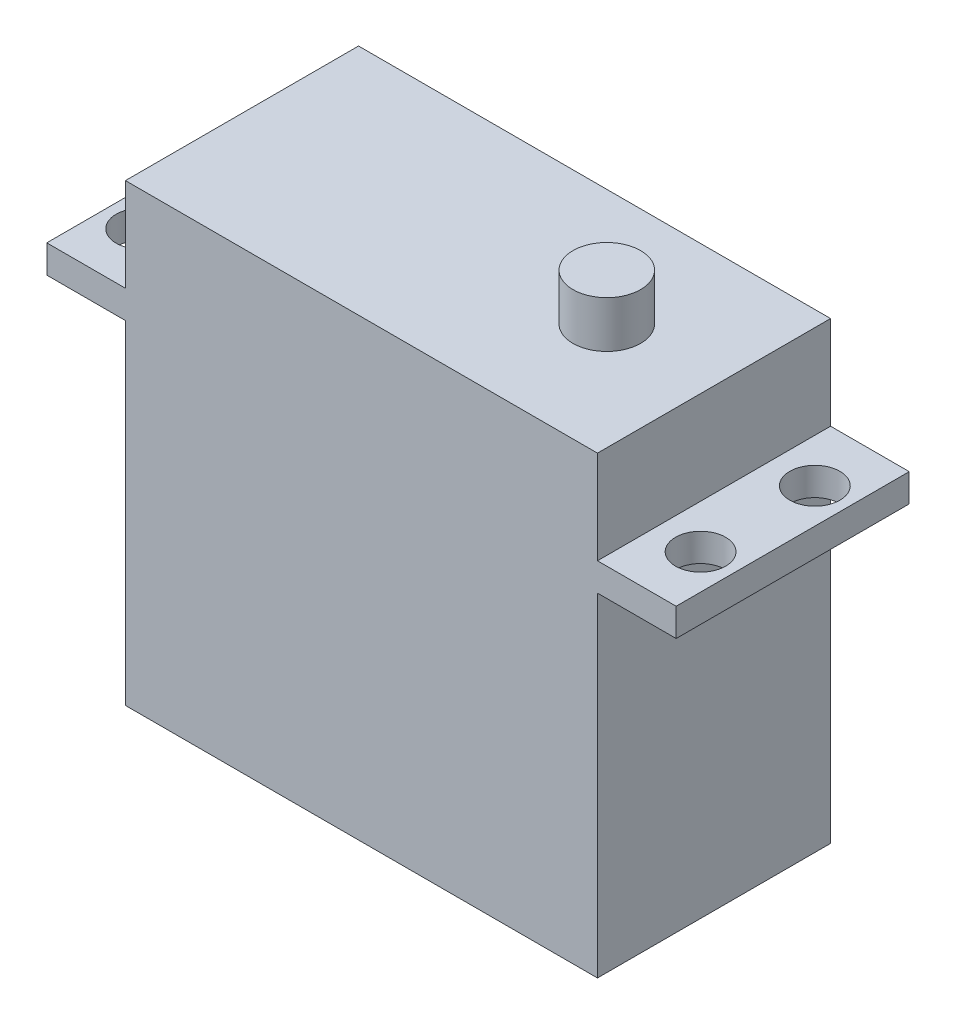
SolidWorks part; units mm, degrees
ref_plane "前视基准面" through (0, 0, 0) normal (0, 0, 1) x (1, 0, 0)
ref_plane "上视基准面" through (0, 0, 0) normal (0, 1, 0) x (1, 0, 0)
ref_plane "右视基准面" through (0, 0, 0) normal (1, 0, 0) x (0, 0, -1)
sketch "草图1" plane through (0, 0, 0) normal (0, 1, 0) x (1, 0, 0)
  line L1 (-20.25, 10) -> (20.25, 10)
  line L2 (-20.25, 10) -> (-20.25, -10)
  line L3 (-20.25, -10) -> (20.25, -10)
  line L4 (20.25, 10) -> (20.25, -10)
  line L5 (-20.25, 10) -> (20.25, -10) construction
  line L6 (-20.25, -10) -> (20.25, 10) construction
  point P0 (0, 0)
  dimension "D1" = 40.5
  dimension "D2" = 20
extrude "凸台-拉伸1" add sketch "草图1" along normal blind 28.6
sketch "草图2" plane through (0, 28.6, 0) normal (0, 1, 0) x (1, 0, 0)
  line L1 (-27, 10) -> (27, 10)
  line L2 (-27, 10) -> (-27, -10)
  line L3 (-27, -10) -> (27, -10)
  line L4 (27, 10) -> (27, -10)
  line L5 (-27, 10) -> (27, -10) construction
  line L6 (-27, -10) -> (27, 10) construction
  point P0 (0, 0)
  dimension "D1" = 54
  dimension "D2" = 20
extrude "凸台-拉伸2" add sketch "草图2" along normal blind 2.4
sketch "草图3" plane through (0, 31, 0) normal (0, 1, 0) x (1, 0, 0)
  line L1 (-20.25, 10) -> (20.25, 10)
  line L2 (-20.25, 10) -> (-20.25, -10)
  line L3 (-20.25, -10) -> (20.25, -10)
  line L4 (20.25, 10) -> (20.25, -10)
  line L5 (-20.25, 10) -> (20.25, -10) construction
  line L6 (-20.25, -10) -> (20.25, 10) construction
  point P0 (0, 0)
  dimension "D1" = 40.5
  dimension "D2" = 20
extrude "凸台-拉伸3" add sketch "草图3" along normal blind 8
sketch "草图4" plane through (0, 39, 0) normal (0, 1, 0) x (1, 0, 0)
  line L0 (0, 0) -> (32.7123, 0) construction
  line L1 (20.25, -10) -> (20.25, 10) construction
  circle A0 centre (11.05, 0) radius 2.9
  dimension "D1" = 5.8
  dimension "D2" = 9.2
extrude "凸台-拉伸4" add sketch "草图4" along normal blind 4
sketch "草图5" plane through (0, 31, 0) normal (0, 1, 0) x (1, 0, 0)
  line L0 (0, 0) -> (0, 17.0393) construction
  line L1 (0, 0) -> (35.0935, 0) construction
  circle A0 centre (24, 4.9) radius 2.15
  circle A1 centre (24, -4.9) radius 2.15
  circle A2 centre (-24, -4.9) radius 2.15
  circle A3 centre (-24, 4.9) radius 2.15
  point P6 (0, 0)
  point P15 (0, 0)
  point P16 (-24.0853, 6.3434)
  dimension "D1" = 4.3
  dimension "D2" = 48
  dimension "D3" = 9.8
extrude "切除-拉伸1" cut sketch "草图5" against normal through all
